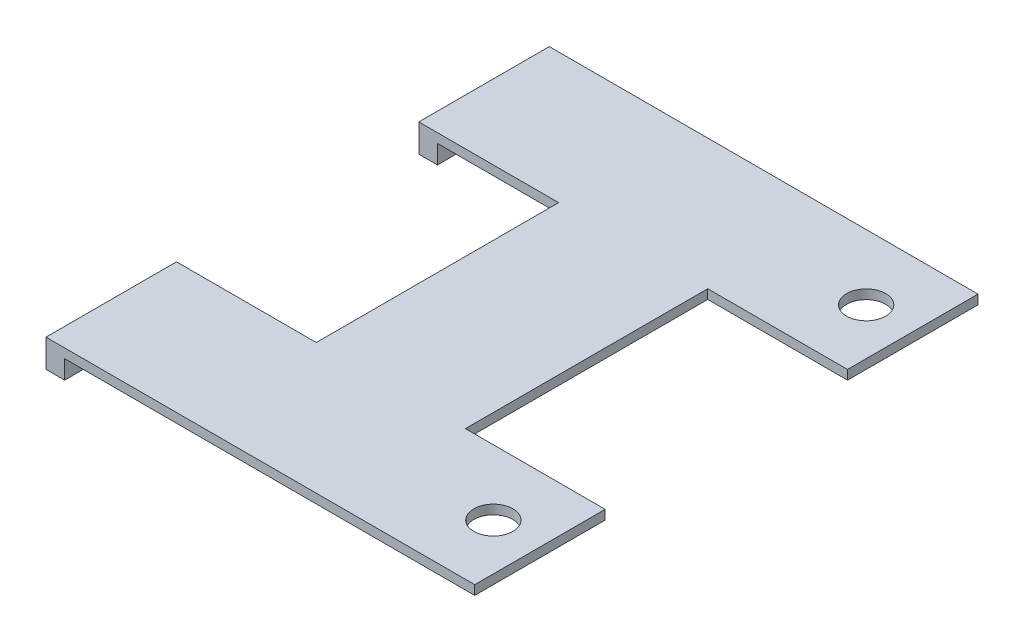
SolidWorks part; units mm, degrees
ref_plane "Front Plane" through (0, 0, 0) normal (0, 0, 1) x (1, 0, 0)
ref_plane "Top Plane" through (0, 0, 0) normal (0, 1, 0) x (1, 0, 0)
ref_plane "Right Plane" through (0, 0, 0) normal (1, 0, 0) x (0, 0, -1)
sketch "Sketch1" plane through (0, 0, 0) normal (0, 1, 0) x (1, 0, 0)
  line L0 (-40.5516, -179.3604) -> (-30.5516, -179.3604) construction
  line L2 (-30.5516, -179.3604) -> (-30.5516, -165.3604) construction
  line L3 (-30.5516, -125.3604) -> (-32.676, -125.3604) construction
  line L6 (-30.5516, -125.3604) -> (-76.5516, -125.3604)
  line L7 (-30.5516, -125.3604) -> (-30.5516, -139.3604)
  line L8 (-30.5516, -179.3604) -> (-76.5516, -179.3604)
  line L9 (-76.5516, -125.3604) -> (-76.5516, -139.3604)
  line L10 (-32.5516, -139.3604) -> (-30.5516, -139.3604) construction
  line L12 (-32.5516, -165.3604) -> (-30.5516, -165.3604) construction
  line L13 (-30.5516, -165.3604) -> (-45.5516, -165.3604)
  line L14 (-30.5516, -139.3604) -> (-45.5516, -139.3604)
  line L15 (-45.5516, -139.3604) -> (-45.5516, -165.3604)
  line L16 (-53.5516, -125.3604) -> (-53.5516, -179.3604) construction
  line L17 (-76.5516, -165.3604) -> (-61.5516, -165.3604)
  line L18 (-76.5516, -139.3604) -> (-61.5516, -139.3604)
  line L19 (-61.5516, -139.3604) -> (-61.5516, -165.3604)
  line L20 (-76.5516, -165.3604) -> (-76.5516, -179.3604)
  line L21 (-30.5516, -139.3604) -> (-30.5516, -125.3604) construction
  line L22 (-30.5516, -165.3604) -> (-30.5516, -179.3604)
  circle A1 centre (-35.5516, -132.3604) radius 2.1
  circle A2 centre (-35.5516, -172.3604) radius 2.1
  dimension "D2" = 15
  dimension "D3" = 15
extrude "Boss-Extrude1" add sketch "Sketch1" along normal blind 1
sketch "Sketch2" plane through (0, 0, 0) normal (0, -1, 0) x (-1, 0, 0)
  line L0 (61.5516, -165.3604) -> (76.5516, -165.3604) construction
  line L1 (76.5516, -179.3604) -> (74.5516, -179.3604)
  line L2 (76.5516, -179.3604) -> (76.5516, -165.3604)
  line L3 (76.5516, -165.3604) -> (74.5516, -165.3604)
  line L4 (74.5516, -179.3604) -> (74.5516, -165.3604)
  line L5 (30.5516, -125.3604) -> (76.5516, -125.3604) construction
  line L6 (76.5516, -139.3604) -> (74.5516, -139.3604)
  line L7 (76.5516, -139.3604) -> (76.5516, -125.3604)
  line L8 (76.5516, -125.3604) -> (74.5516, -125.3604)
  line L9 (74.5516, -139.3604) -> (74.5516, -125.3604)
  dimension "D1" = 2
  dimension "D2" = 2
extrude "Boss-Extrude2" add sketch "Sketch2" along normal blind 2
